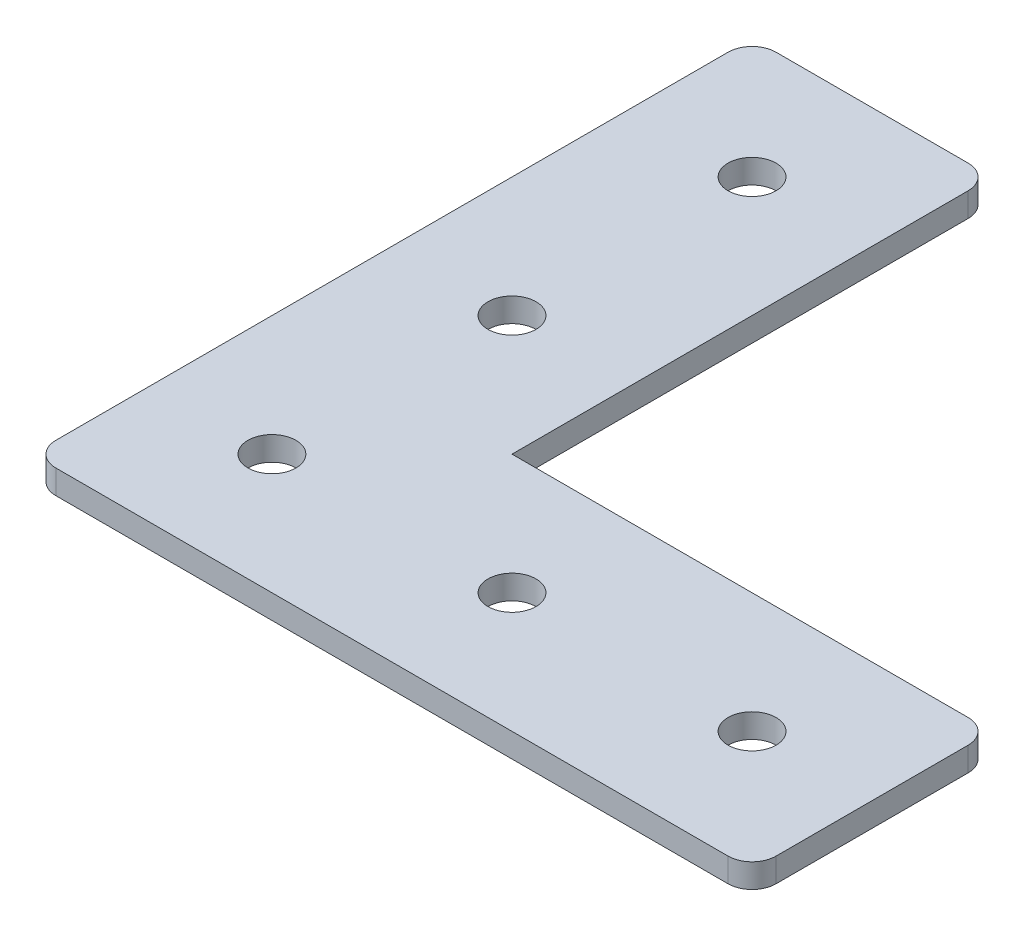
SolidWorks part; units mm, degrees
ref_plane "Front Plane" through (0, 0, 0) normal (0, 0, 1) x (1, 0, 0)
ref_plane "Top Plane" through (0, 0, 0) normal (0, 1, 0) x (1, 0, 0)
ref_plane "Right Plane" through (0, 0, 0) normal (1, 0, 0) x (0, 0, -1)
sketch "Sketch1" plane through (0, 0, 0) normal (0, 1, 0) x (1, 0, 0)
  line L0 (25.4, 76.2) -> (25.4, 25.4)
  line L1 (0, 0) -> (76.2, 0)
  line L2 (0, 0) -> (0, 76.2)
  line L3 (0, 76.2) -> (25.4, 76.2)
  line L4 (76.2, 0) -> (76.2, 25.4)
  line L5 (25.4, 25.4) -> (76.2, 25.4)
  circle A0 centre (12.7, 12.7) radius 2.54
  circle A1 centre (38.1, 12.7) radius 2.54
  circle A2 centre (63.5, 12.7) radius 2.54
  circle A3 centre (12.7, 38.1) radius 2.54
  circle A4 centre (12.7, 63.5) radius 2.54
  dimension "D6" = 5.08
  dimension "D1" = 76.2
  dimension "D2" = 76.2
  dimension "D3" = 25.4
  dimension "D4" = 25.4
  dimension "D5" = 50.8
  dimension "D7" = 12.7
  dimension "D8" = 12.7
  dimension "D9" = 3
  dimension "D10" = 3
extrude "Boss-Extrude1" add sketch "Sketch1" along normal blind 2.54
fillet "Fillet1" radius 2.54 5 edges at (0, 1.27, 0) (76.2, 1.27, 0) (76.2, 1.27, -25.4) (25.4, 1.27, -76.2) (0, 1.27, -76.2)
